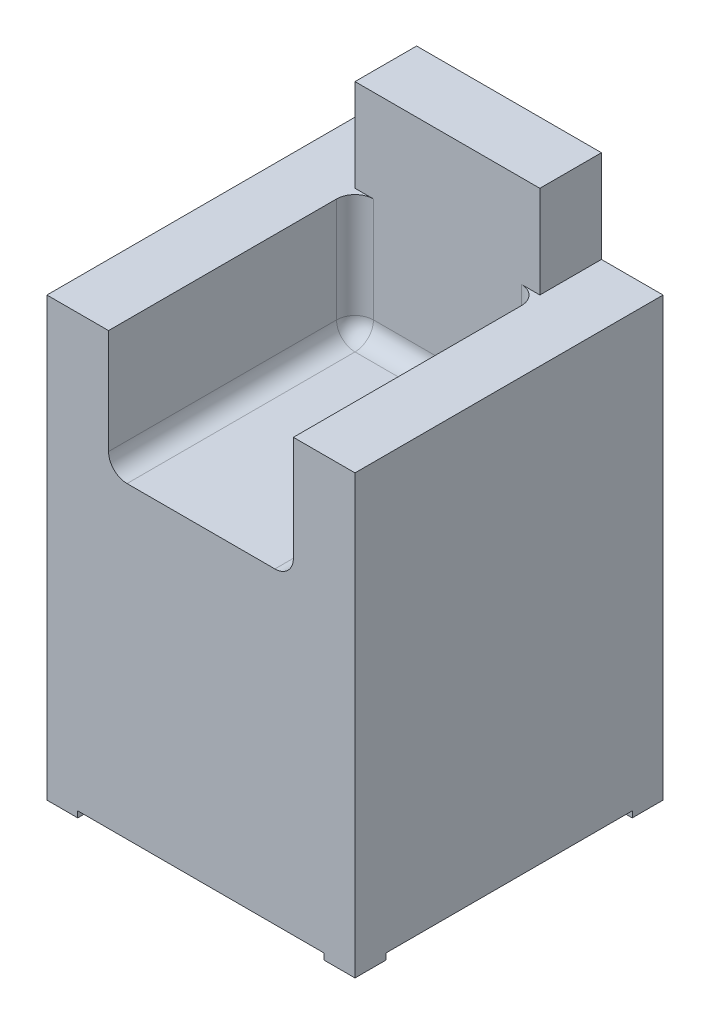
SolidWorks part; units mm, degrees
ref_plane "Front Plane" through (0, 0, 0) normal (0, 0, 1) x (1, 0, 0)
ref_plane "Top Plane" through (0, 0, 0) normal (0, 1, 0) x (1, 0, 0)
ref_plane "Right Plane" through (0, 0, 0) normal (1, 0, 0) x (0, 0, -1)
sketch "Sketch1" plane through (0, 0, 0) normal (0, 1, 0) x (1, 0, 0)
  line L0 (0, 0) -> (-500, 0)
  line L1 (-500, 0) -> (-500, -500)
  line L2 (-500, -500) -> (0, -500)
  line L3 (0, -500) -> (0, 0)
  dimension "D1" = 500
  dimension "D2" = 500
extrude "Boss-Extrude1" add sketch "Sketch1" along normal mid plane 500
sketch "Sketch2" plane through (0, 250, 0) normal (0, 1, 0) x (1, 0, 0)
  line L0 (-500, 0) -> (-500, -100)
  line L1 (-500, 0) -> (-500, -500) construction
  line L2 (-500, -100) -> (0, -100)
  line L3 (0, -500) -> (0, 0) construction
  line L4 (0, -100) -> (0, 0)
  line L5 (0, 0) -> (-500, 0)
  dimension "D1" = 100
extrude "Boss-Extrude2" add sketch "Sketch2" along normal blind 350
sketch "Sketch3" plane through (0, 250, 0) normal (0, 1, 0) x (1, 0, 0)
  line L0 (-500, -100) -> (-500, -500)
  line L1 (-500, -500) -> (-400, -500)
  line L2 (-500, -500) -> (0, -500) construction
  line L3 (-400, -500) -> (-400, -100)
  line L4 (-500, -100) -> (0, -100) construction
  line L5 (-400, -100) -> (-500, -100)
  dimension "D1" = 100
extrude "Boss-Extrude3" add sketch "Sketch3" along normal blind 200
sketch "Sketch4" plane through (0, 250, 0) normal (0, 1, 0) x (1, 0, 0)
  line L0 (0, -100) -> (-100, -100)
  line L1 (-400, -100) -> (0, -100) construction
  line L2 (-100, -100) -> (-100, -500)
  line L3 (-400, -500) -> (0, -500) construction
  line L4 (-100, -500) -> (0, -500)
  line L5 (0, -500) -> (0, -100)
  dimension "D1" = 100
extrude "Boss-Extrude4" add sketch "Sketch4" along normal blind 200
sketch "Sketch5" plane through (0, 0, 100) normal (0, 0, 1) x (1, 0, 0)
  line L0 (-500, 600) -> (-400, 600)
  line L1 (-500, 600) -> (0, 600) construction
  line L2 (-400, 600) -> (-400, 450)
  line L3 (-400, 450) -> (-500, 450)
  line L4 (-500, 600) -> (-500, 450) construction
  line L5 (-500, 450) -> (-500, 600)
  dimension "D1" = 150
  dimension "D2" = 100
extrude "Cut-Extrude4" cut sketch "Sketch5" against normal blind 200
sketch "Sketch8" plane through (0, 0, 100) normal (0, 0, 1) x (1, 0, 0)
  line L0 (-100, 450) -> (0, 450)
  line L1 (0, 450) -> (0, 600)
  line L2 (0, 600) -> (-100, 600)
  line L3 (-400, 600) -> (0, 600) construction
  line L4 (-100, 600) -> (-100, 450)
extrude "Cut-Extrude5" cut sketch "Sketch8" against normal blind 200
fillet "Fillet4" radius 30 1 edges at (-400, 250, 300)
fillet "Fillet5" radius 30 1 edges at (-100, 250, 300)
fillet "Fillet6" radius 30 5 edges at (-400, 365, 100) (-391.2132, 258.7868, 100) (-100, 365, 100) (-108.7868, 258.7868, 100) (-250, 250, 100)
sketch "Sketch9" plane through (0, -250, 0) normal (0, -1, 0) x (1, 0, 0)
  line L0 (-500, 500) -> (-500, 450)
  line L1 (-500, 0) -> (-500, 500) construction
  line L2 (-500, 450) -> (-450, 450)
  line L3 (-450, 450) -> (-450, 500)
  line L4 (-500, 500) -> (0, 500) construction
  line L5 (-450, 500) -> (-500, 500)
  line L6 (-500, 0) -> (-450, 0)
  line L7 (0, 0) -> (-500, 0) construction
  line L8 (-450, 0) -> (-450, 50)
  line L9 (-450, 50) -> (-500, 50)
  line L10 (-500, 50) -> (-500, 0)
  line L11 (0, 0) -> (0, 50)
  line L12 (0, 500) -> (0, 0) construction
  line L13 (0, 50) -> (-50, 50)
  line L14 (-50, 50) -> (-50, 0)
  line L15 (-50, 0) -> (0, 0)
  line L16 (0, 500) -> (-50, 500)
  line L17 (-50, 500) -> (-50, 450)
  line L18 (-50, 450) -> (0, 450)
  line L19 (0, 450) -> (0, 500)
  dimension "D1" = 50
  dimension "D2" = 50
  dimension "D3" = 50
  dimension "D4" = 50
  dimension "D5" = 50
  dimension "D6" = 50
  dimension "D7" = 50
  dimension "D8" = 50
extrude "Boss-Extrude5" add sketch "Sketch9" along normal blind 10 contours L5 L0 L2 L3 | L19 L16 L17 L18 | L10 L6 L8 L9 | L15 L11 L13 L14
